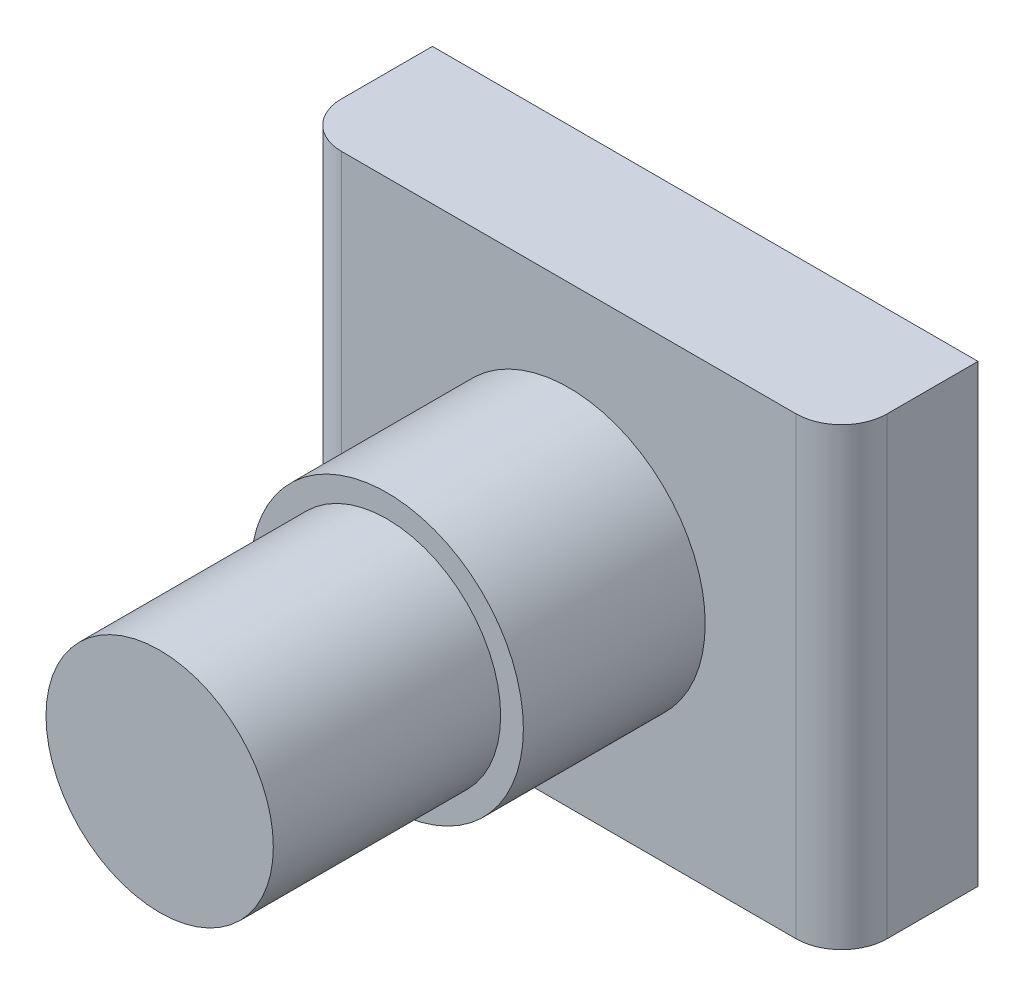
SolidWorks part; units mm, degrees
ref_plane "Front Plane" through (0, 0, 0) normal (0, 0, 1) x (1, 0, 0)
ref_plane "Top Plane" through (0, 0, 0) normal (0, 1, 0) x (1, 0, 0)
ref_plane "Right Plane" through (0, 0, 0) normal (1, 0, 0) x (0, 0, -1)
sketch "Sketch2" plane through (0, 0, 0) normal (0, 0, 1) x (1, 0, 0)
  line L1 (-6, 5) -> (6, 5)
  line L2 (-6, 5) -> (-6, -5)
  line L3 (-6, -5) -> (6, -5)
  line L4 (6, 5) -> (6, -5)
  line L5 (-6, 5) -> (6, -5) construction
  line L6 (-6, -5) -> (6, 5) construction
  point P0 (0, 0)
  dimension "D1" = 10
  dimension "D2" = 12
extrude "Boss-Extrude1" add sketch "Sketch2" along normal blind 3
sketch "Sketch3" plane through (0, 0, 0) normal (1, 0, 0) x (0, 0, -1)
  line L0 (-3, 0) -> (-3, 3)
  line L1 (-3, -5) -> (-3, 5) construction
  line L2 (-3, 3) -> (-7, 3)
  line L3 (-7, 3) -> (-7, 2.5)
  line L4 (-7, 2.5) -> (-12, 2.5)
  line L5 (-12, 2.5) -> (-12, 0)
  line L6 (55, 0) -> (-55, 0) construction
  line L7 (-12, 0) -> (-3, 0)
  dimension "D1" = 4
  dimension "D2" = 5
  dimension "D3" = 2.5
  dimension "D4" = 3
revolve "Revolve1" add sketch "Sketch3" angle 360 about L7
fillet "Fillet1" radius 1 2 edges at (6, 0, 3) (-6, 0, 3)
